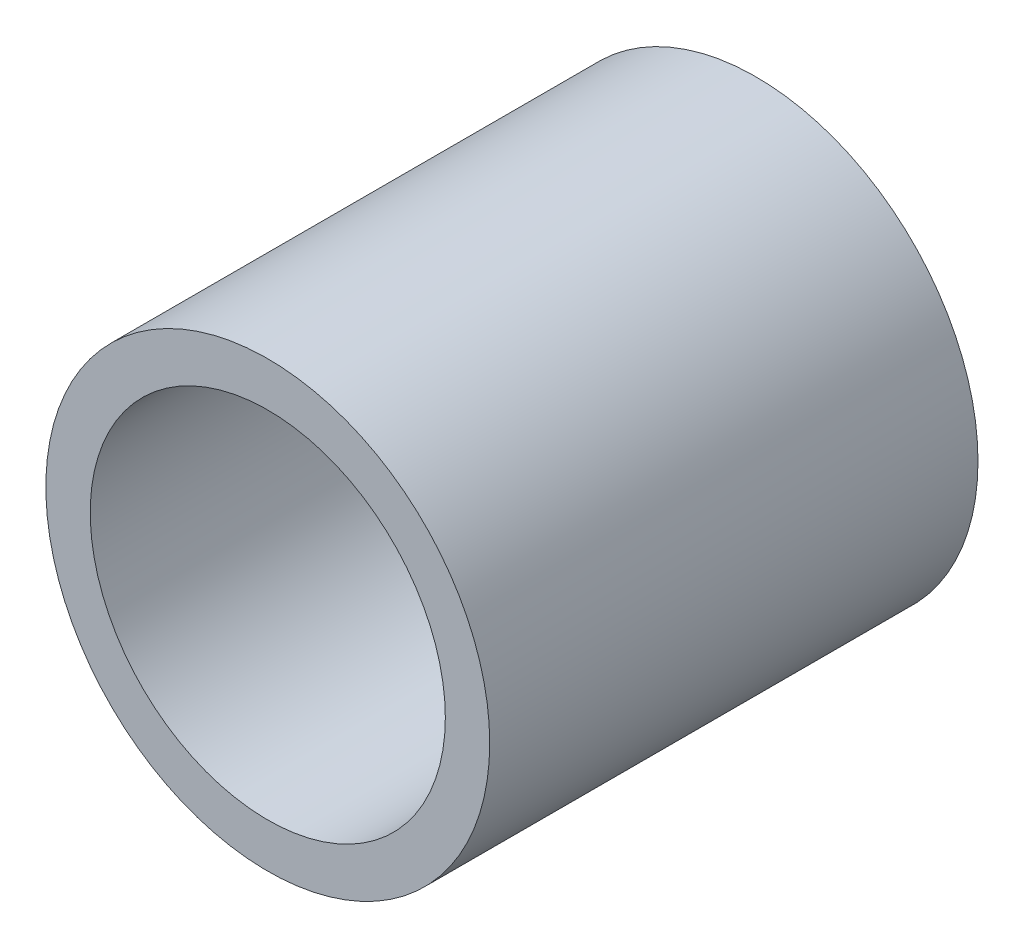
SolidWorks part; units mm, degrees
ref_plane "Front Plane" through (0, 0, 0) normal (0, 0, 1) x (1, 0, 0)
ref_plane "Top Plane" through (0, 0, 0) normal (0, 1, 0) x (1, 0, 0)
ref_plane "Right Plane" through (0, 0, 0) normal (1, 0, 0) x (0, 0, -1)
sketch "Sketch1" plane through (0, 0, 0) normal (0, 0, 1) x (1, 0, 0)
  circle A0 centre (0, 0) radius 0.625
  circle A1 centre (0, 0) radius 0.5
  dimension "D1" = 1.25
  dimension "D2" = 1
extrude "Boss-Extrude1" add sketch "Sketch1" along normal blind 1.375
